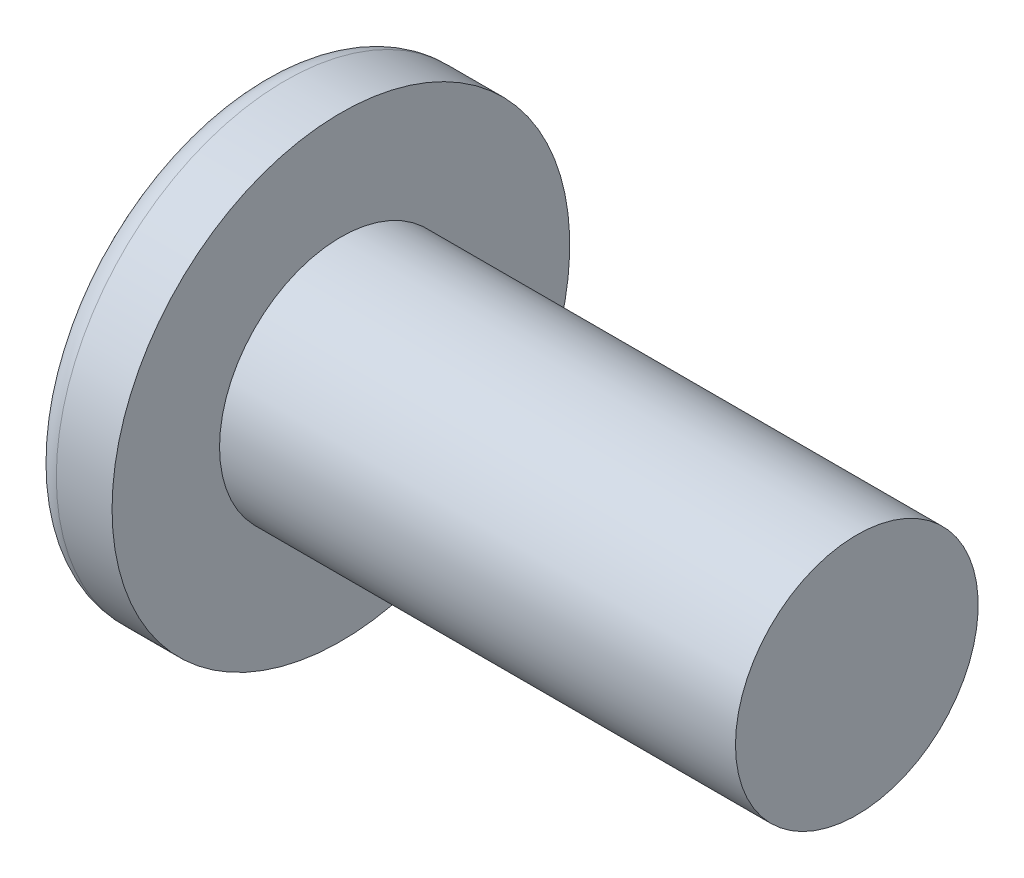
SolidWorks part; units mm, degrees
ref_plane "Plane1" through (0, 0, 0) normal (0, 0, 1) x (1, 0, 0)
ref_plane "Plane2" through (0, 0, 0) normal (0, 1, 0) x (1, 0, 0)
ref_plane "Plane3" through (0, 0, 0) normal (1, 0, 0) x (0, 0, -1)
sketch "BodySke" plane through (0, 0, 0) normal (0, 0, 1) x (1, 0, 0)
  line L0 (1.9, 1.75) -> (1.9, 3.3)
  line L1 (2.4, 6.35) -> (2.4, -3.175) construction
  line L2 (-25.4, 0) -> (127, 0) construction
  line L3 (9.34, 0) -> (0, 0)
  line L4 (1.9, 1.75) -> (9.34, 1.75)
  line L5 (9.34, 1.75) -> (9.34, 0)
  line L6 (1.096, 3.3) -> (1.9, 3.3)
  line L7 (1.9, -1.75) -> (9.34, -1.75) construction
  line L8 (1.9, 6.35) -> (1.9, -3.175) construction
  arc A0 (0.7785, 3.1096) -> (0, 0) centre (6.6, 0) ccw
  arc A2 (0.7785, 3.1096) -> (1.096, 3.3) centre (1.096, 2.94) cw
  dimension "Head_crown_rad" = 6.6
  dimension "Head_fillet_rad" = 0.36
  dimension "Diameter" = 3.5
  dimension "Length" = 7.44
  dimension "Head_ht" = 1.9
  dimension "Head_dia" = 6.6
  dimension "Advance" = 0.5
  dimension "Thread_nom" = 7.44
revolve "Base-Revolve" add sketch "BodySke" angle 360 about L2
cosmetic thread "ThreadCosmetic" [suppressed] parameters "Thread_length"=6.94, "Thread_minor"=2.439
sketch "Sketch3" plane through (0, 0, 0) normal (1, 0, 0) x (0, 0, -1)
  line L0 (0.37, -1.45) -> (-0.37, -1.45)
  line L1 (0.37, -1.45) -> (0.37, 1.45)
  line L2 (-0.37, 1.45) -> (0.37, 1.45)
  line L3 (-0.37, 1.45) -> (-0.37, -1.45)
  dimension "Cross_dia" = 2.9
  dimension "D1" = 1.45
  dimension "Cross_width" = 0.74
  dimension "D2" = 0.37
ref_plane "Plane4" through (1.76, 0, 0) normal (1, 0, 0) x (0, 0, -1)
sketch "Sketch4" plane through (1.76, 0, 0) normal (1, 0, 0) x (0, 0, -1)
  line L0 (0.185, -0.185) -> (-0.185, -0.185)
  line L1 (0.185, -0.185) -> (0.185, 0.185)
  line L2 (-0.185, 0.185) -> (0.185, 0.185)
  line L3 (-0.185, 0.185) -> (-0.185, -0.185)
  dimension "D2" = 0.37
  dimension "D1" = 0.37
  dimension "D3" = 0.185
  dimension "D4" = 0.185
loft "Cut-Loft1" cut profiles "Sketch3", "Sketch4"
pattern_circular "CirPattern1" count 2 every 90 about axis through (0, 0, 0) along (1, 0, 0) of "Cut-Loft1"
sketch "ThdSchSke" plane through (0, 0, 0) normal (0, 0, 1) x (1, 0, 0)
  line L0 (2.4, -1.2195) -> (2.0285, -1.75)
  line L1 (2.4, -1.2195) -> (2.7715, -1.75)
  line L2 (2.7715, -1.75) -> (2.7715, -2.1875)
  line L3 (-3.175, 0) -> (5.1513, 0) construction
  line L5 (2.7715, -2.1875) -> (2.0285, -2.1875)
  line L6 (2.0285, -2.1875) -> (2.0285, -1.75)
  dimension "Diameter" = 3.5
  dimension "SideAngle" = 55
  dimension "VeeAngle" = 70
  dimension "Thread_minor" = 2.439
  dimension "Overcut" = 4.375
  dimension "Start" = 2.4
revolve "ThreadSchematic" [suppressed] cut sketch "ThdSchSke" angle 360 about L3
pattern_linear "ThdSchPat" [suppressed]
equation "\"D1@Sketch3\" = \"Cross_dia@Sketch3\" / 2"
equation "\"D2@Sketch3\" = \"Cross_width@Sketch3\" / 2"
equation "\"D1@Sketch4\" = \"Cross_width@Sketch3\" *.5"
equation "\"D2@Sketch4\" = \"D1@Sketch4\""
equation "\"D3@Sketch4\" = \"D1@Sketch4\" / 2"
equation "\"D4@Sketch4\" = \"D2@Sketch4\" / 2"
equation "\"Thread_length@ThreadCosmetic\" = ((sgn( (\"Length@BodySke\" - \"Advance@BodySke\" ) - \"Thread_nom@BodySke\" )-1)*( (\"Length@BodySke\" - \"Advance@BodySke\" ) - \"Thread_nom@BodySke\" ))/-2+ \"Thread_nom@BodySke\""
equation "\"Thread_minor@ThdSchSke\" = \"Thread_minor@ThreadCosmetic\""
equation "\"Diameter@ThdSchSke\" = \"Diameter@BodySke\""
equation "\"Overcut@ThdSchSke\" = \"Diameter@BodySke\" * 1.25"
equation "\"Start@ThdSchSke\" = \"Head_ht@BodySke\" + \"Length@BodySke\" - \"Thread_length@ThreadCosmetic\"  '---Non-countersunk---"
equation "\"Num_threads@ThdSchPat\" = int( \"Thread_length@ThreadCosmetic\" / \"Advance@BodySke\" + 0.999 )  + 1"
equation "\"Advance@ThdSchPat\" = \"Thread_length@ThreadCosmetic\" /  (\"Num_threads@ThdSchPat\" - 1) 'relax it"
